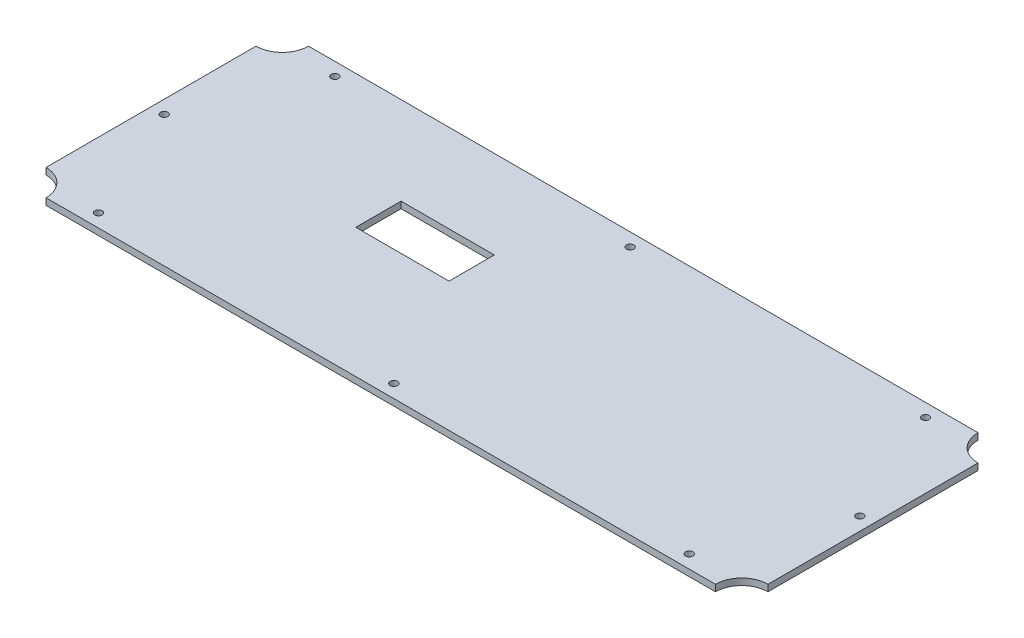
SolidWorks part; units mm, degrees
other "Thermal 1"
material "6061 Alloy"
ref_plane "Front Plane" through (0, 0, 0) normal (0, 0, 1) x (1, 0, 0)
ref_plane "Top Plane" through (0, 0, 0) normal (0, 1, 0) x (1, 0, 0)
ref_plane "Right Plane" through (0, 0, 0) normal (1, 0, 0) x (0, 0, -1)
sketch "Sketch3" plane through (0, 0, 0) normal (0, 1, 0) x (1, 0, 0)
  line L1 (139.7, 50.8) -> (-139.7, 50.8)
  line L2 (139.7, 50.8) -> (139.7, -50.8)
  line L3 (139.7, -50.8) -> (-139.7, -50.8)
  line L4 (-139.7, 50.8) -> (-139.7, -50.8)
  line L5 (139.7, 50.8) -> (-139.7, -50.8) construction
  line L6 (139.7, -50.8) -> (-139.7, 50.8) construction
  point P0 (0, 0)
  dimension "D1" = 279.4
  dimension "D2" = 101.6
extrude "Rectangle cut" add sketch "Sketch3" against normal blind 5.08
sketch "Sketch4" plane through (0, 0, 0) normal (0, 1, 0) x (1, 0, 0)
  circle A0 centre (-139.7, -50.8) radius 10.16
extrude "Cut-Extrude2" cut sketch "Sketch4" against normal blind 7.62
mirror "mountingCorners" about plane through (0, 0, 0) normal (1, 0, 0) of "Cut-Extrude2"
mirror "Mirror3" about plane through (0, 0, 0) normal (0, 0, 1) of "mountingCorners", "Cut-Extrude2"
sketch "Sketch6" plane through (0, 0, 0) normal (0, 1, 0) x (1, 0, 0)
  line L0 (-139.7, 40.64) -> (-139.7, -40.64) construction
  line L1 (-59.69, 16.764) -> (-23.622, 16.764)
  line L2 (-59.69, 16.764) -> (-59.69, -0.762)
  line L3 (-59.69, -0.762) -> (-23.622, -0.762)
  line L4 (-23.622, 16.764) -> (-23.622, -0.762)
  line L5 (129.54, 50.8) -> (-129.54, 50.8) construction
  point P6 (-41.656, 16.764)
  dimension "D1" = 80.01
  dimension "D2" = 36.068
  dimension "D3" = 17.526
  dimension "D4" = 34.036
extrude "Cut-Extrude3" cut sketch "Sketch6" against normal blind 7.62
sketch "Sketch9" plane through (0, -5.08, 0) normal (0, -1, 0) x (1, 0, 0)
  line L5 (129.286, 40.386) -> (-129.286, -40.386) construction
  line L9 (-164.814, 60.7823) -> (164.814, 60.7823)
  line L10 (-164.814, 60.7823) -> (-164.814, -60.7823)
  line L11 (-164.814, -60.7823) -> (164.814, -60.7823)
  line L12 (164.814, 60.7823) -> (164.814, -60.7823)
  line L13 (-164.814, 60.7823) -> (164.814, -60.7823) construction
  line L14 (-164.814, -60.7823) -> (164.814, 60.7823) construction
  point P0 (0, 0)
  point P10 (0, 0)
extrude "Cut-Extrude5" cut sketch "Sketch9" against normal blind 2.54
sketch "Sketch11" plane through (0, -2.54, 0) normal (0, -1, 0) x (1, 0, 0)
  line L0 (129.54, -50.8) -> (-129.54, -50.8) construction
  line L1 (-139.7, -40.64) -> (-139.7, 40.64) construction
  circle A0 centre (-114.3, -45.72) radius 1.4224
  dimension "D1" = 5.08
  dimension "D2" = 2.8448
  dimension "D3" = 25.4
extrude "Cut-Extrude6" cut sketch "Sketch11" against normal blind 2.54
mirror "Mirror4" about plane through (0, 0, 0) normal (0, 0, 1) of "Cut-Extrude6" second plane through (0, 0, 0) second plane normal (1, 0, 0)
sketch "Sketch12" plane through (0, -2.54, 0) normal (0, -1, 0) x (1, 0, 0)
  line L0 (-139.7, -40.64) -> (-139.7, 40.64) construction
  line L1 (129.54, -50.8) -> (-129.54, -50.8) construction
  circle A0 centre (-134.62, 0) radius 1.4224
  dimension "D1" = 5.08
  dimension "D2" = 50.8
  dimension "D3" = 2.8448
extrude "Cut-Extrude7" cut sketch "Sketch12" against normal blind 2.54
mirror "Mirror5" about plane through (0, 0, 0) normal (1, 0, 0) of "Cut-Extrude7"
sketch "Sketch13" plane through (0, -2.54, 0) normal (0, -1, 0) x (1, 0, 0)
  line L0 (129.54, -50.8) -> (-129.54, -50.8) construction
  circle A0 centre (0, -45.72) radius 1.4224
  dimension "D1" = 5.08
  dimension "D2" = 2.8448
extrude "Cut-Extrude8" cut sketch "Sketch13" against normal blind 2.54
mirror "Mirror6" about plane through (0, 0, 0) normal (0, 0, 1) of "Cut-Extrude8"
